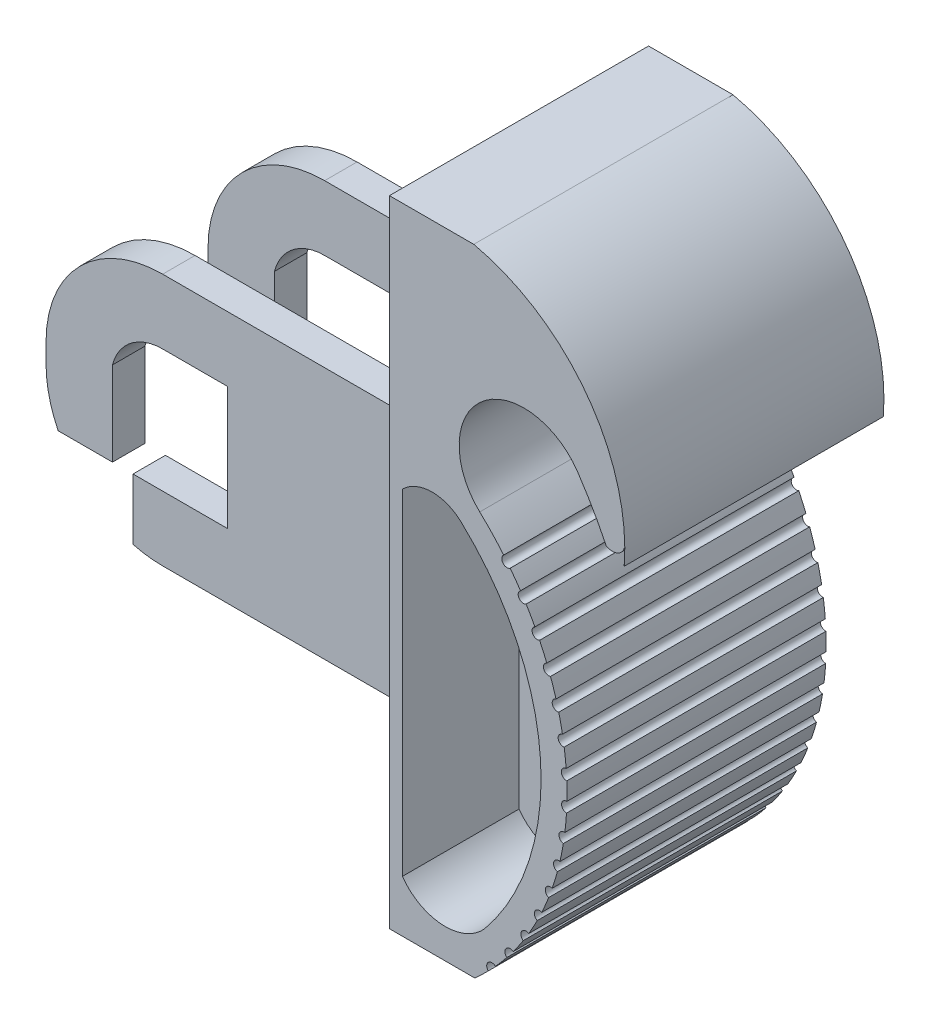
SolidWorks part; units mm, degrees
material "PE Alta densidad"
ref_plane "Alzado" through (0, 0, 0) normal (0, 0, 1) x (1, 0, 0)
ref_plane "Planta" through (0, 0, 0) normal (0, 1, 0) x (1, 0, 0)
ref_plane "Vista lateral" through (0, 0, 0) normal (1, 0, 0) x (0, 0, -1)
sketch "Croquis1" plane through (0, 0, 0) normal (0, 0, 1) x (1, 0, 0)
  line L1 (-15, 24.5) -> (15, 24.5)
  line L2 (-15, 24.5) -> (-15, -24.5)
  line L3 (-15, -24.5) -> (15, -24.5)
  line L4 (15, 24.5) -> (15, -24.5)
  line L5 (-15, 24.5) -> (15, -24.5) construction
  line L6 (-15, -24.5) -> (15, 24.5) construction
  point P0 (0, 0)
  dimension "D1" = 30
  dimension "D2" = 49
extrude "Saliente-Extruir1" add sketch "Croquis1" along normal blind 20
sketch "Croquis2" plane through (0, 0, 20) normal (0, 0, 1) x (1, 0, 0)
  line L0 (-15, 24.5) -> (-15, -24.5) construction
  line L1 (-10, 11.5) -> (-9.5173, 11.5)
  line L2 (-10, 24.5) -> (-10, -24.5) construction
  line L3 (-10, 10.5) -> (-9.6183, 10.5)
  line L5 (-15, 10.5) -> (-15, -24.5)
  line L6 (-3, 5.7691) -> (-3, -0.3248)
  line L8 (15, -24.5) -> (15, 24.5)
  line L9 (15, 24.5) -> (-15, 24.5)
  line L10 (-15, 24.5) -> (-15, -24.5)
  line L11 (-15, -24.5) -> (15, -24.5)
  line L12 (15, -24.5) -> (15, 24.5)
  line L13 (15, 24.5) -> (-15, 24.5)
  line L14 (-15, 10.5) -> (-15, -24.5)
  line L15 (-15, -24.5) -> (15, -24.5)
  line L16 (-10, 11.5) -> (-10, 8.4727)
  line L17 (-3, 10.5) -> (-3, -24.5) construction
  arc A1 (-8.4163, -24.5) -> (-10, 8.4727) centre (-22.4935, -8.6518) ccw
  arc A2 (-10, 8.5024) -> (-8.7356, 7.663) centre (-6.6345, 12.2001) ccw
  arc A3 (-0.4745, 13.298) -> (-8.03, 6.8447) centre (-4.6183, 10.5) ccw
  arc A5 (-15, 24.5) -> (2.8395, 6.8447) centre (-11.7445, 9.949) cw
  arc A6 (2.8395, 6.8447) -> (-0.4745, 13.298) centre (-25.6952, -3.7315) ccw
  dimension "D2" = 10
  dimension "D4" = 10
  dimension "D1" = 0
  dimension "D3" = 12
  dimension "D5" = 5
extrude "Cortar-Extruir3" cut sketch "Croquis2" against normal blind 20
sketch "Croquis3" plane through (0, 0, 20) normal (0, 0, 1) x (1, 0, 0)
  line L0 (3.1643, 10.1849) -> (3.1413, 10.1849)
  line L1 (3.1413, 10.1849) -> (3.1209, 8.7877)
  line L2 (3.1209, 8.7877) -> (2.8395, 6.8447)
  line L3 (2.8395, 6.8447) -> (1.2664, 10.3808)
  line L4 (1.2614, 10.2829) -> (2.8395, 6.8447)
  arc A0 (3.1643, 10.1849) -> (1.2664, 10.3808) centre (2.2154, 10.2829) cw
  arc A1 (2.8395, 6.8447) -> (-8.4891, 24.5) centre (-11.7445, 9.949) ccw construction
  arc A2 (2.8395, 6.8447) -> (-0.4745, 13.298) centre (-25.6952, -3.7315) ccw construction
extrude "Cortar-Extruir5" cut sketch "Croquis3" against normal blind 20 contours L1 A0 L3 L2
sketch "Croquis4" plane through (2.9922, -0.0436, 0) normal (-0.9999, 0.0146, 0) x (0, 0, 1)
  line L0 (19.9649, 10.0791) -> (20.1848, 6.9815)
  line L1 (20.1848, 6.9815) -> (0, 6.9815)
  line L2 (0, 6.9815) -> (0, 10.0896)
  line L3 (0, 10.0896) -> (19.9649, 10.0791)
extrude "Cortar-Extruir6" cut sketch "Croquis4" along normal blind 0.3
ref_plane "Plano1" through (2.8534, 6.9407, 20) normal (0, 0, -1) x (-1, 0, 0)
sketch "Croquis5" plane through (2.8534, 6.9407, 20) normal (0, 0, -1) x (-1, 0, 0)
  line L1 (0.0584, 0.2837) -> (-13.1754, 0.2837)
  line L2 (0.0584, 0.2837) -> (0.0584, -2.1196)
  line L3 (0.0584, -2.1196) -> (-13.1754, -2.1196)
  line L4 (-13.1754, 0.2837) -> (-13.1754, -2.1196)
extrude "Cortar-Extruir9" cut sketch "Croquis5" along direction (0, 0, 1) on the side of the normal blind 20.3
sketch "Croquis6" plane through (-15, 0, 0) normal (-1, 0, 0) x (0, 0, 1)
  line L10 (20, -11.5) -> (0, -11.5)
  line L11 (17.5, -11.5) -> (15, -11.5)
  line L12 (5, 19.5) -> (5, -19.5)
  line L13 (5, -19.5) -> (15, -19.5)
  line L14 (15, -19.5) -> (15, 19.5)
  line L15 (15, 19.5) -> (5, 19.5)
  line L16 (5, 8) -> (5, -11.5)
  line L18 (15, -11.5) -> (15, 8)
  line L20 (17.5, -11.5) -> (17.5, 8)
  line L21 (20, 8) -> (0, 8)
  line L22 (17.5, 8) -> (15, 8)
  line L23 (2.5, 8) -> (2.5, -11.5)
  line L25 (5, 8) -> (2.5, 8)
  line L26 (5, -11.5) -> (2.5, -11.5)
  dimension "D2" = 13
  dimension "D1" = 5
  dimension "D3" = 16.5
  dimension "D4" = 2.5
extrude "Saliente-Extruir2" add sketch "Croquis6" along normal blind 29
fillet "Redondeo1" radius 9 4 edges at (-44, 8, 16.25) (-44, -11.5, 16.25) (-44, -11.5, 3.75) (-44, 8, 3.75)
sketch "Croquis7" plane through (0, 0, 2.5) normal (0, 0, -1) x (-1, 0, 0)
  line L0 (37.2881, -11.2043) -> (37.2881, -6.5)
  line L1 (38.873, 0) -> (38.873, -10.624)
  line L2 (30, 8) -> (30, -11.5)
  line L3 (30, 3) -> (30, -6.5)
  line L4 (30.873, 0) -> (30.873, -10.624)
  line L5 (30, -6.5) -> (38.873, -6.5)
  line L6 (37.2881, 2.2809) -> (37.2881, 7.7043)
  line L7 (15, -11.5) -> (35, -11.5)
  line L8 (15, -11.5) -> (35, -11.5)
  line L12 (20, -6.5) -> (35, -6.5)
  line L13 (39, -2.5) -> (39, -1)
  line L14 (35, 3) -> (20, 3)
  line L15 (20, 3) -> (20, -6.5)
  line L16 (30, -6.5) -> (35, -6.5)
  line L17 (39, -2.5) -> (39, -1)
  line L18 (35, 3) -> (30, 3)
  line L20 (0, -26.5) -> (35, -26.5)
  line L21 (59, -2.5) -> (59, -1)
  line L22 (35, 23) -> (0, 23)
  line L23 (0, 23) -> (0, -26.5)
  line L24 (0, -26.5) -> (35, -26.5)
  line L26 (35, 23) -> (0, 23)
  line L27 (0, 23) -> (0, -26.5)
  line L29 (35, -3.5) -> (15, -3.5)
  line L30 (35, -3.5) -> (15, -3.5)
  arc A0 (35, -11.5) -> (44, -2.5) centre (35, -2.5) ccw construction
  arc A1 (44, -1) -> (35, 8) centre (35, -1) ccw construction
  arc A4 (35, -26.5) -> (59, -2.5) centre (35, -2.5) ccw
  arc A5 (59, -1) -> (35, 23) centre (35, -1) ccw
  arc A6 (35, -6.5) -> (39, -2.5) centre (35, -2.5) ccw
  arc A7 (39, -1) -> (35, 3) centre (35, -1) ccw
  arc A9 (39, -1) -> (35, 3) centre (35, -1) ccw
  arc A13 (35, -11.5) -> (44, -2.5) centre (35, -2.5) ccw
  arc A14 (35, -11.5) -> (44, -2.5) centre (35, -2.5) ccw
  dimension "D1" = 5
  dimension "D2" = 15
  dimension "D3" = 15
  dimension "D4" = 8
  dimension "D5" = 8
  dimension "D6" = 0
extrude "Cortar-Extruir10" cut sketch "Croquis7" against normal blind 29
sketch "Croquis8" plane through (0, 0, 2.5) normal (0, 0, -1) x (-1, 0, 0)
  line L0 (30, -6.5) -> (43.0623, -6.5)
  line L18 (38.873, 0) -> (38.873, -10.624)
  line L19 (44, -2.5) -> (44, -1)
  line L20 (35, 8) -> (15, 8)
  line L21 (15, 8) -> (15, -11.5)
  line L22 (15, -11.5) -> (35, -11.5)
  line L23 (37.2881, -11.2043) -> (37.2881, -6.5)
  line L24 (37.2881, -6.5) -> (30, -6.5)
  line L25 (30, -6.5) -> (30, 3)
  line L26 (30, 3) -> (35, 3)
  line L27 (38.873, 0) -> (38.873, -10.624)
  line L28 (44, -2.5) -> (44, -1)
  line L29 (35, 8) -> (15, 8)
  line L30 (15, 8) -> (15, -11.5)
  line L31 (15, -11.5) -> (35, -11.5)
  line L32 (37.2881, -11.2043) -> (37.2881, -6.5)
  line L33 (37.2881, -6.5) -> (30, -6.5)
  line L34 (30, -6.5) -> (30, 3)
  line L35 (30, 3) -> (35, 3)
  arc A8 (38.873, -10.624) -> (44, -2.5) centre (35, -2.5) ccw
  arc A9 (44, -1) -> (35, 8) centre (35, -1) ccw
  arc A10 (35, -11.5) -> (37.2881, -11.2043) centre (35, -2.5) ccw
  arc A11 (38.873, 0) -> (35, 3) centre (35, -1) ccw
  arc A12 (38.873, -10.624) -> (44, -2.5) centre (35, -2.5) ccw
  arc A13 (44, -1) -> (35, 8) centre (35, -1) ccw
  arc A14 (35, -11.5) -> (37.2881, -11.2043) centre (35, -2.5) ccw
  arc A15 (38.873, 0) -> (35, 3) centre (35, -1) ccw
  dimension "D1" = 0
extrude "Cortar-Extruir11" cut sketch "Croquis8" against normal blind 29 contours L0 L18
sketch "Croquis9" plane through (0, 0, 0) normal (0, 0, -1) x (-1, 0, 0)
  line L2 (14, 24.5) -> (14, -24.5)
  line L3 (14, 24.5) -> (14, -24.5)
  line L4 (15, -20.5) -> (8.4163, -20.5)
  line L5 (15, -20.5) -> (8.4163, -20.5)
  arc A0 (8.3556, -24.4438) -> (14.1834, -26.4916) centre (13.5035, -19.1098) ccw
  arc A1 (14, -20.5) -> (7.3884, -20.5) centre (10.6942, -18.1321) cw
  arc A2 (9.3946, 5.3826) -> (14, 5.3826) centre (11.6973, 3.0799) cw
  arc A3 (9.7445, -23.0047) -> (14, -24.5) centre (13.5035, -19.1098) ccw
  arc A4 (9.3946, 5.3826) -> (9.7445, -23.0047) centre (22.4935, -8.6518) ccw
  arc A5 (9.3946, 5.3826) -> (-1.183, 14.4172) centre (4.6183, 10.5) ccw
  arc A6 (9.3946, 5.3826) -> (9.7445, -23.0047) centre (22.4935, -8.6518) ccw
  arc A7 (9.3946, 5.3826) -> (-1.183, 14.4172) centre (4.6183, 10.5) ccw
  dimension "D1" = 1
  dimension "D2" = 2
  dimension "D3" = 2
  dimension "D4" = 4
extrude "Cortar-Extruir16" cut sketch "Croquis9" against normal blind 9
sketch "Croquis11" plane through (0, 0, 9) normal (0, 0, -1) x (-1, 0, 0)
  line L2 (14, -20.5) -> (14, 5.3826)
  line L3 (14, -20.5) -> (14, 5.3826)
  arc A8 (9.3946, 5.3826) -> (9.5054, 5.4884) centre (4.6183, 10.5) ccw
  arc A9 (9.3946, 5.3826) -> (7.6699, -20.8503) centre (22.4935, -8.6518) ccw
  arc A10 (7.6699, -20.8503) -> (14, -20.5) centre (10.6942, -18.1321) ccw
  arc A11 (14, 5.3826) -> (9.5054, 5.4884) centre (11.6973, 3.0799) ccw
  arc A12 (9.3946, 5.3826) -> (9.5054, 5.4884) centre (4.6183, 10.5) ccw
  arc A13 (9.3946, 5.3826) -> (7.6699, -20.8503) centre (22.4935, -8.6518) ccw
  arc A14 (7.6699, -20.8503) -> (14, -20.5) centre (10.6942, -18.1321) ccw
  arc A15 (14, 5.3826) -> (9.5054, 5.4884) centre (11.6973, 3.0799) ccw
  dimension "D1" = 0
extrude "Cortar-Extruir17" cut sketch "Croquis11" against normal blind 9 from offset 2 offset against normal yes
sketch "Croquis13" plane through (0, 0, 0) normal (0, 0, -1) x (-1, 0, 0)
  circle A0 centre (5.928, 4.5739) radius 0.4014
  arc A1 (8.03, 6.8447) -> (8.4163, -24.5) centre (22.4935, -8.6518) ccw construction
extrude "Cortar-Extruir18" cut sketch "Croquis13" against normal blind 22
pattern_circular "MatrizC1" count 15 over 82 about axis through (-22.4935, -8.6518, 0) along (0, 0, 1) of "Cortar-Extruir18"
